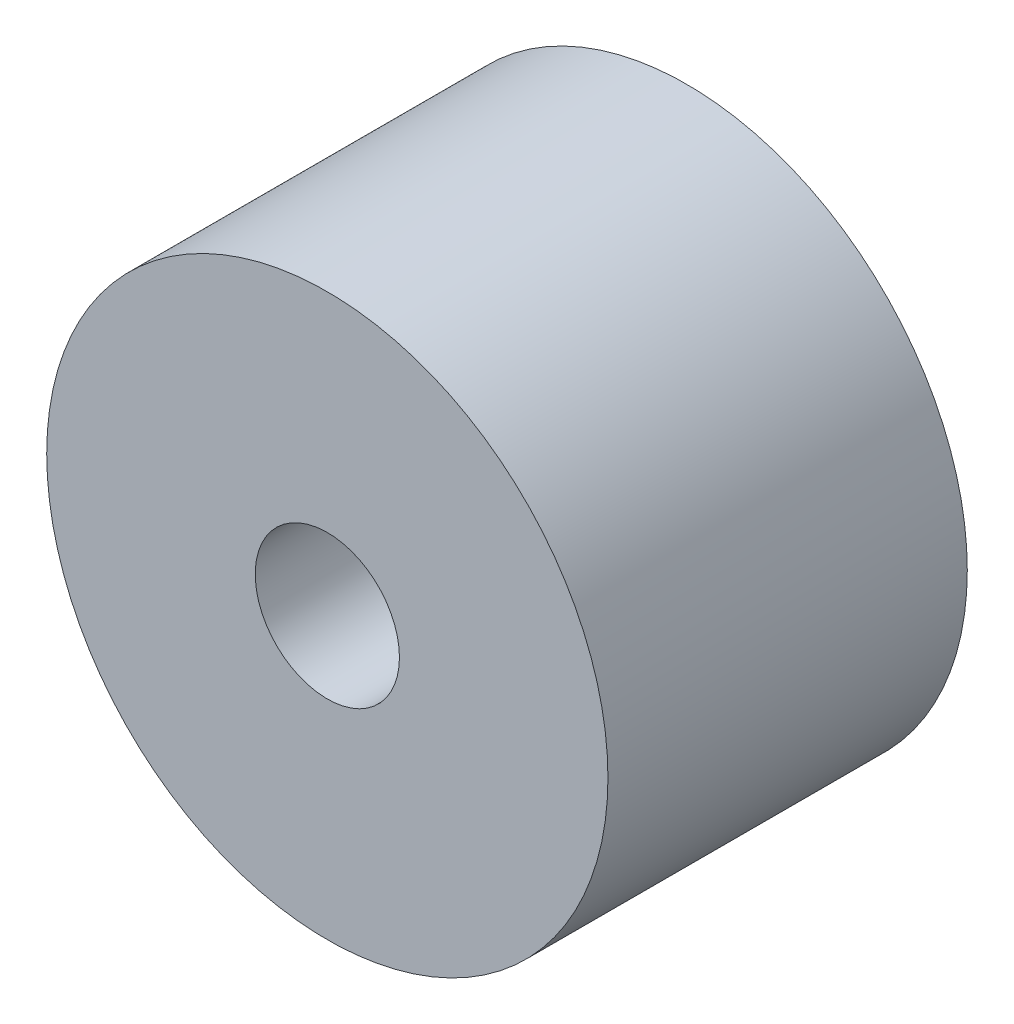
SolidWorks part; units mm, degrees
ref_plane "Front Plane" through (0, 0, 0) normal (0, 0, 1) x (1, 0, 0)
ref_plane "Top Plane" through (0, 0, 0) normal (0, 1, 0) x (1, 0, 0)
ref_plane "Right Plane" through (0, 0, 0) normal (1, 0, 0) x (0, 0, -1)
sketch "Sketch1" plane through (0, 0, 0) normal (0, 0, 1) x (1, 0, 0)
  circle A0 centre (0, 0) radius 2.335
  circle A1 centre (0, 0) radius 0.6
  dimension "D1" = 4.67
  dimension "D2" = 1.2
extrude "Boss-Extrude1" add sketch "Sketch1" along normal blind 2.99
